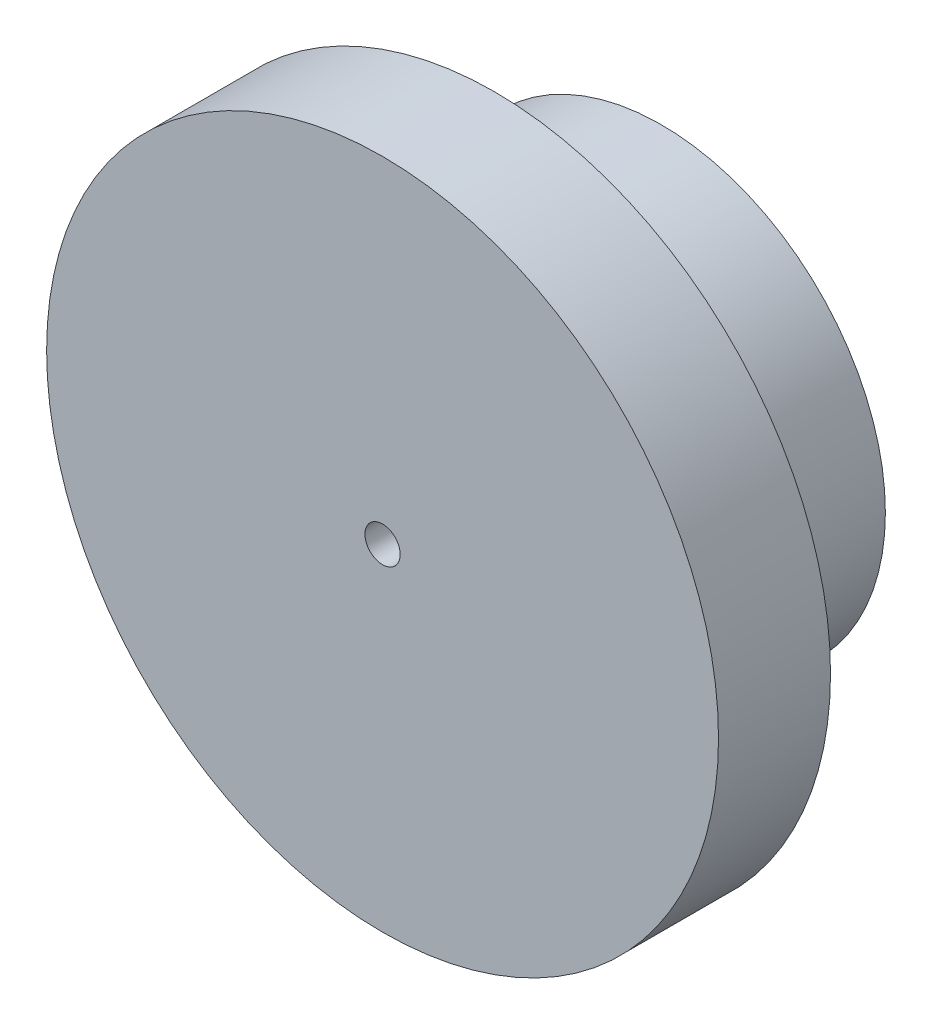
SolidWorks part; units mm, degrees
ref_plane "Front Plane" through (0, 0, 0) normal (0, 0, 1) x (1, 0, 0)
ref_plane "Top Plane" through (0, 0, 0) normal (0, 1, 0) x (1, 0, 0)
ref_plane "Right Plane" through (0, 0, 0) normal (1, 0, 0) x (0, 0, -1)
sketch "Sketch2" plane through (0, 0, 0) normal (0, 0, 1) x (1, 0, 0)
  circle A0 centre (0, 0) radius 12.7
  dimension "D1" = 25.4
extrude "Boss-Extrude1" add sketch "Sketch2" along normal blind 6.35 and the other way up to vertex (3.1115 mm away)
sketch "Sketch4" plane through (0, 0, 6.35) normal (0, 0, 1) x (1, 0, 0)
  circle A0 centre (0, 0) radius 19.05
  circle A1 centre (0, 0) radius 1
  dimension "D1" = 38.1
extrude "Boss-Extrude2" add sketch "Sketch4" along normal blind 6.35
sketch "Sketch5" plane through (0, 0, -3.1115) normal (0, 0, -1) x (-1, 0, 0)
  circle A0 centre (0, 0) radius 11
extrude "Cut-Extrude1" cut sketch "Sketch5" against normal blind 7
